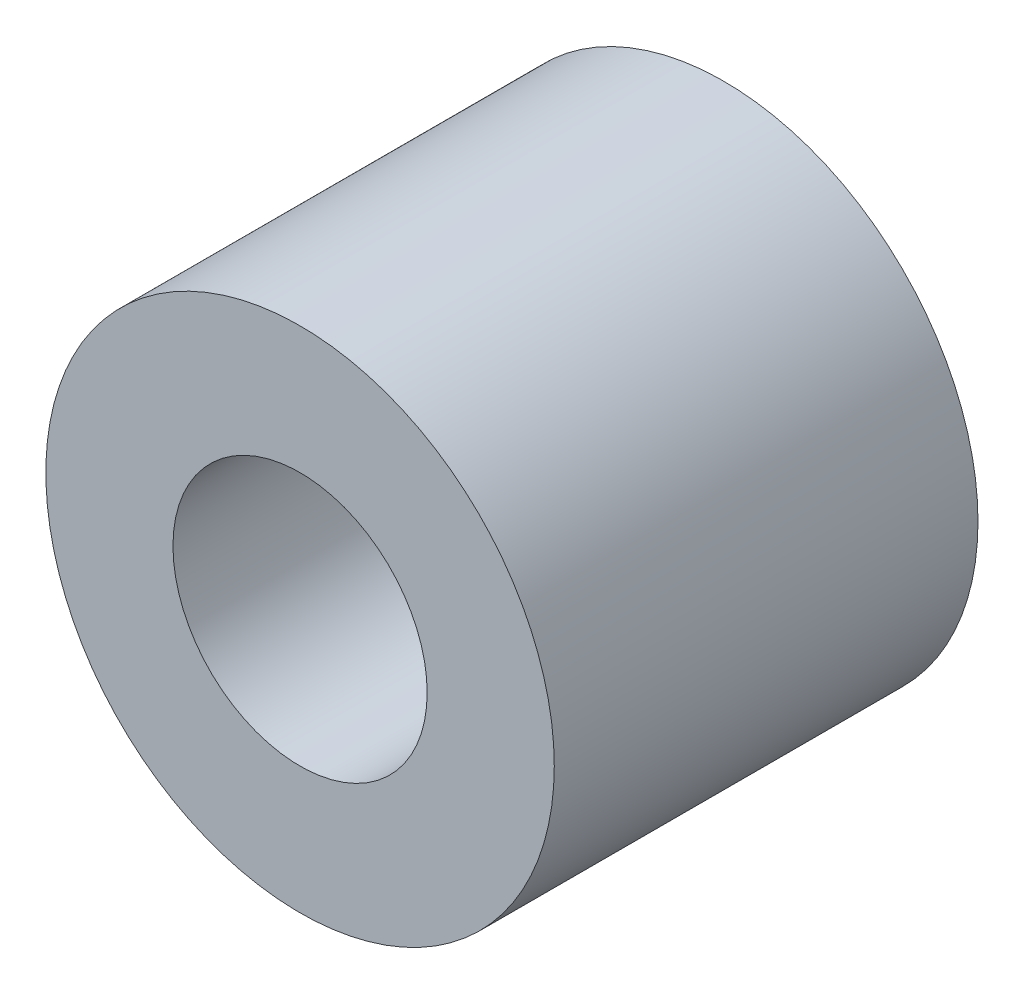
SolidWorks part; units mm, degrees
ref_plane "Front Plane" through (0, 0, 0) normal (0, 0, 1) x (1, 0, 0)
ref_plane "Top Plane" through (0, 0, 0) normal (0, 1, 0) x (1, 0, 0)
ref_plane "Right Plane" through (0, 0, 0) normal (1, 0, 0) x (0, 0, -1)
sketch "Sketch1" plane through (0, 0, 0) normal (0, 0, 1) x (1, 0, 0)
  circle A0 centre (0, 0) radius 30
  circle A1 centre (0, 0) radius 15
  dimension "D1" = 60
  dimension "D2" = 30
extrude "Boss-Extrude1" add sketch "Sketch1" along normal mid plane 50
